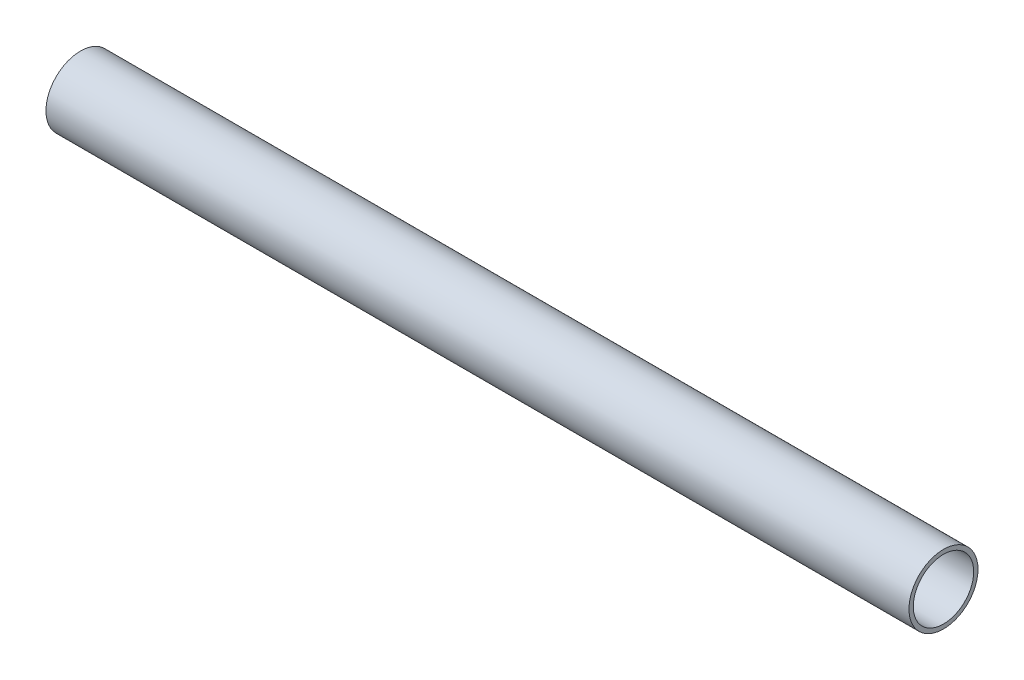
SolidWorks part; units mm, degrees
material "ABS"
ref_plane "Front" through (0, 0, 0) normal (0, 0, 1) x (1, 0, 0)
ref_plane "Top" through (0, 0, 0) normal (0, 1, 0) x (1, 0, 0)
ref_plane "Right" through (0, 0, 0) normal (1, 0, 0) x (0, 0, -1)
sketch "草图1" plane through (0, 0, 0) normal (1, 0, 0) x (0, 0, -1)
  circle A0 centre (0, 0) radius 17.5
  circle A1 centre (0, 0) radius 20
  dimension "D1" = 35
  dimension "D2" = 40
extrude "凸台-拉伸1" add sketch "草图1" along normal blind 500
